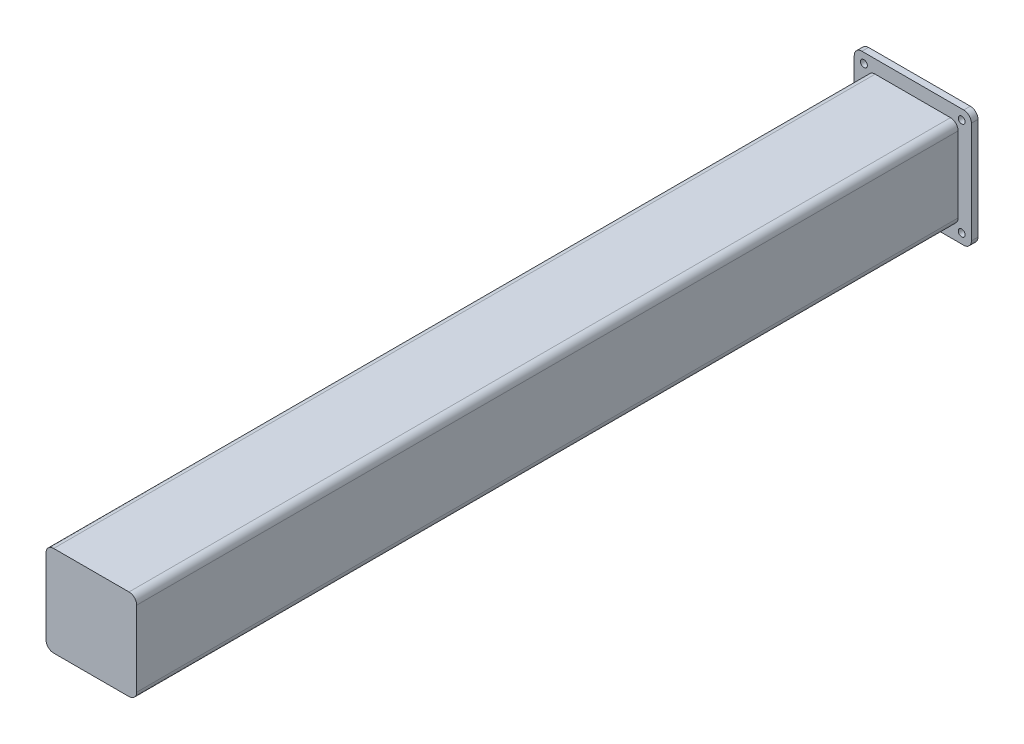
SolidWorks part; units mm, degrees
material "Plain Carbon Steel"
ref_plane "Front Plane" through (0, 0, 0) normal (0, 0, 1) x (1, 0, 0)
ref_plane "Top Plane" through (0, 0, 0) normal (0, 1, 0) x (1, 0, 0)
ref_plane "Right Plane" through (0, 0, 0) normal (1, 0, 0) x (0, 0, -1)
sketch "Sketch1" plane through (0, 0, 0) normal (0, 0, 1) x (1, 0, 0)
  line L1 (-57.5, -57.5) -> (57.5, -57.5)
  line L2 (-57.5, -57.5) -> (-57.5, 57.5)
  line L3 (-57.5, 57.5) -> (57.5, 57.5)
  line L4 (57.5, -57.5) -> (57.5, 57.5)
  line L5 (-57.5, -57.5) -> (57.5, 57.5) construction
  line L6 (-57.5, 57.5) -> (57.5, -57.5) construction
  point P0 (0, 0)
  dimension "D1" = 115
extrude "Boss-Extrude1" add sketch "Sketch1" along normal blind 6.5
sketch "Sketch2" plane through (0, 0, 6.5) normal (0, 0, 1) x (1, 0, 0)
  line L1 (-44.5, -44.5) -> (44.5, -44.5)
  line L2 (-44.5, -44.5) -> (-44.5, 44.5)
  line L3 (-44.5, 44.5) -> (44.5, 44.5)
  line L4 (44.5, -44.5) -> (44.5, 44.5)
  line L5 (-44.5, -44.5) -> (44.5, 44.5) construction
  line L6 (-44.5, 44.5) -> (44.5, -44.5) construction
  point P0 (0, 0)
  dimension "D1" = 89
extrude "Boss-Extrude2" add sketch "Sketch2" along normal blind 806.45
fillet "Fillet1" radius 7.5 8 edges at (-57.5, 57.5, 3.25) (57.5, 57.5, 3.25) (57.5, -57.5, 3.25) (-57.5, -57.5, 3.25) (-44.5, -44.5, 409.725) (44.5, -44.5, 409.725) (-44.5, 44.5, 409.725) (44.5, 44.5, 409.725)
sketch "Sketch3" plane through (0, 0, 6.5) normal (0, 0, 1) x (1, 0, 0)
  line L0 (50, 57.5) -> (-50, 57.5) construction
  line L1 (-57.5, 50) -> (-57.5, -50) construction
  line L2 (-50, -57.5) -> (50, -57.5) construction
  line L3 (57.5, -50) -> (57.5, 50) construction
  circle A0 centre (48, 48) radius 3.3782
  circle A1 centre (48, -48) radius 3.3782
  circle A2 centre (-48, 48) radius 3.3782
  circle A3 centre (-48, -48) radius 3.3782
  dimension "D1" = 9.5
  dimension "D5" = 6.7564
  dimension "D2" = 9.5
  dimension "D3" = 9.5
  dimension "D4" = 9.5
extrude "Cut-Extrude1" cut sketch "Sketch3" against normal up to surface (6.5 mm away) contours A1 | A2 | A0 | A3 up to face at (0, 0, 0)
ref_plane "Plane1" [suppressed] through (0, 0, 0) normal (0, -1, 0) x (-1, 0, 0)
ref_plane "Plane2" [suppressed] through (0, 0, 0) normal (1, 0, 0) x (0, 0, -1)
shell "Shell1" thickness 5
